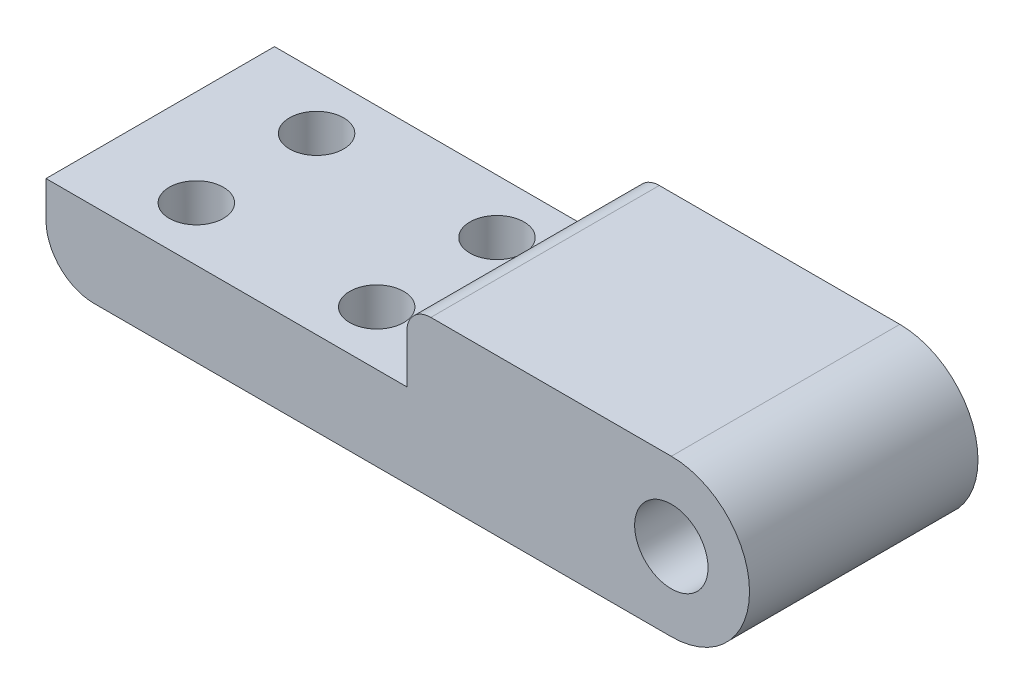
SolidWorks part; units mm, degrees
ref_plane "前视基准面" through (0, 0, 0) normal (0, 0, 1) x (1, 0, 0)
ref_plane "上视基准面" through (0, 0, 0) normal (0, 1, 0) x (1, 0, 0)
ref_plane "右视基准面" through (0, 0, 0) normal (1, 0, 0) x (0, 0, -1)
sketch "草图1" plane through (0, 0, 0) normal (0, 0, 1) x (1, 0, 0)
  line L1 (1.729, 8.951) -> (23.729, 8.951)
  line L2 (-28.271, 2.951) -> (-28.271, -4.049)
  line L3 (-28.271, -4.049) -> (23.729, -4.049)
  line L7 (-28.271, 2.951) -> (1.729, 2.951)
  line L8 (1.729, 8.951) -> (1.729, 2.951)
  arc A0 (23.729, -4.049) -> (23.729, 8.951) centre (23.729, 2.451) ccw
  circle A1 centre (23.729, 2.451) radius 3.05
  dimension "D3" = 6.1
  dimension "D1" = 7
  dimension "D2" = 13
  dimension "D4" = 52
  dimension "D5" = 30
extrude "凸台-拉伸1" add sketch "草图1" along normal blind 19
sketch "草图2" plane through (0, 2.951, 0) normal (0, 1, 0) x (1, 0, 0)
  line L0 (-30.6108, -9.5) -> (33.2635, -9.5) construction
  line L1 (1.729, -19) -> (-28.271, -19) construction
  line L2 (1.729, 0) -> (-28.271, 0) construction
  line L3 (-28.271, -19) -> (-28.271, 0) construction
  circle A0 centre (-20.271, -4.5) radius 2.25
  circle A1 centre (-5.271, -4.5) radius 2.25
  circle A2 centre (-5.271, -14.5) radius 2.25
  circle A3 centre (-20.271, -14.5) radius 2.25
  dimension "D1" = 4.5
  dimension "D3" = 15
  dimension "D4" = 8
  dimension "D2" = 5
extrude "切除-拉伸1" cut sketch "草图2" against normal blind 20
fillet "圆角1" radius 4 1 edges at (-28.271, -4.049, 9.5)
fillet "圆角2" radius 2 1 edges at (1.729, 8.951, 9.5)
